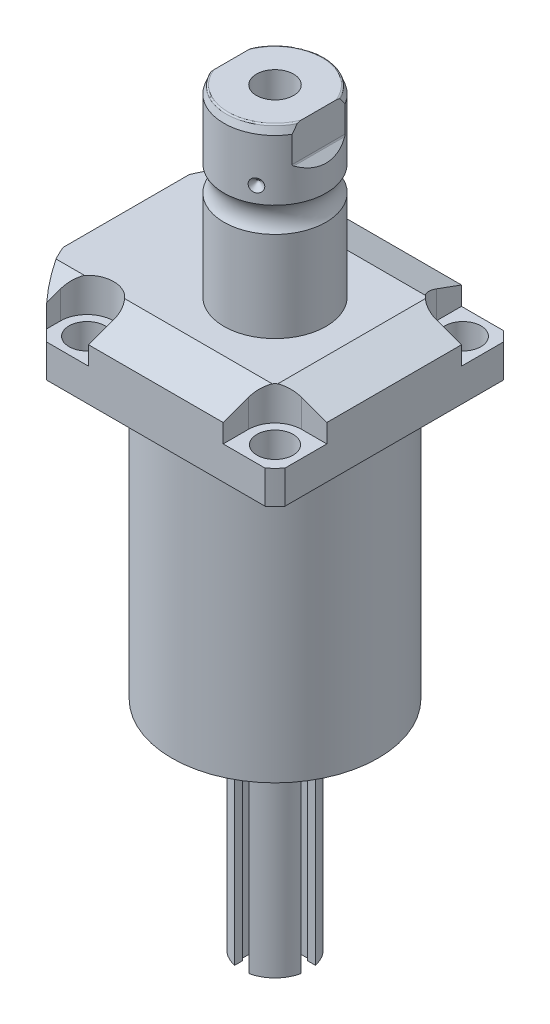
SolidWorks part; units mm, degrees
material "Alloy Steel"
ref_plane "Front Plane" through (0, 0, 0) normal (0, 0, 1) x (1, 0, 0)
ref_plane "Top Plane" through (0, 0, 0) normal (0, 1, 0) x (1, 0, 0)
ref_plane "Right Plane" through (0, 0, 0) normal (1, 0, 0) x (0, 0, -1)
ref_plane "Plane1" through (0, 0, 0) normal (0, 1, 0) x (0, 0, 1)
sketch "Sketch1" plane through (0, 0, 0) normal (0, 1, 0) x (0, 0, 1)
  line L0 (-44.45, 44.45) -> (44.45, 44.45)
  line L1 (44.45, 44.45) -> (44.45, -55.5498)
  line L2 (44.45, -55.5498) -> (-44.45, -55.5498)
  line L3 (-44.45, -55.5498) -> (-44.45, 44.45)
  line L4 (0, 0) -> (0, -60.6467) construction
  dimension "D1" = 55.5498
  dimension "D2" = 99.9998
  dimension "D3" = 88.9
extrude "Extrude1" add sketch "Sketch1" along normal blind 129.794
sketch "Sketch2" plane through (0, 0, 0) normal (0, -1, 0) x (1, 0, 0)
  circle A0 centre (0, 0) radius 60.325
  dimension "D1" = 120.65
extrude "Cut-Extrude1" cut sketch "Sketch2" against normal through all flip side to cut
ref_plane "Plane2" through (0, 0, 0) normal (1, 0, 0) x (0, 0, 1)
sketch "Sketch3" plane through (0, 0, 0) normal (1, 0, 0) x (0, 0, 1)
  line L0 (38.4937, 0) -> (38.4937, -104.775)
  line L1 (38.4937, -104.775) -> (76.5937, -104.775)
  line L2 (76.5937, -104.775) -> (76.5937, 0)
  line L3 (76.5937, 0) -> (38.4937, 0)
  line L4 (0, -93.345) -> (0, 4.445) construction
  line L5 (40.7836, 0) -> (-40.7836, 0) construction
  dimension "D1" = 76.9874
  dimension "D2" = 153.1874
  dimension "D3" = 104.775
revolve "Cut-Revolve1" cut sketch "Sketch3" angle 360 about L4
fillet "Fillet1" radius 0.381 1 edges at (0, 104.775, 38.4937)
sketch "Sketch4" plane through (0, 129.794, 0) normal (0, 1, 0) x (-1, 0, 0)
  line L0 (-44.45, 40.7836) -> (-44.45, -40.7836) construction
  line L1 (40.7836, 44.45) -> (-40.7836, 44.45) construction
  line L2 (-25.1206, -44.45) -> (-25.1206, -35.052)
  line L3 (-44.45, -44.45) -> (-25.1206, -44.45)
  line L4 (-44.45, -25.1206) -> (-44.45, -44.45)
  line L5 (-35.052, -25.1206) -> (-44.45, -25.1206)
  line L6 (44.9834, -44.45) -> (25.1206, -44.45)
  line L7 (25.1206, 44.45) -> (25.1206, 35.052)
  line L8 (44.9834, 44.45) -> (44.9834, 35.052)
  line L9 (44.9834, 44.45) -> (25.1206, 44.45)
  line L10 (-35.052, 25.1206) -> (-44.45, 25.1206)
  line L11 (-44.45, 25.1206) -> (-44.45, 44.45)
  line L12 (-44.45, 44.45) -> (-25.1206, 44.45)
  line L13 (-25.1206, 44.45) -> (-25.1206, 35.052)
  line L14 (-48.9217, 0) -> (49.4551, 0) construction
  line L15 (44.9834, -44.45) -> (44.9834, -35.052)
  line L16 (25.1206, -44.45) -> (25.1206, -35.052)
  arc A0 (25.1206, -35.052) -> (44.9834, -35.052) centre (35.052, -35.052) cw
  arc A1 (-35.052, -25.1206) -> (-25.1206, -35.052) centre (-35.052, -35.052) cw
  arc A2 (-35.052, 25.1206) -> (-25.1206, 35.052) centre (-35.052, 35.052) ccw
  arc A3 (25.1206, 35.052) -> (44.9834, 35.052) centre (35.052, 35.052) ccw
  dimension "D2" = 9.9314
  dimension "D1" = 35.052
  dimension "D3" = 35.052
  dimension "D4" = 35.052
extrude "Cut-Extrude2" cut sketch "Sketch4" against normal blind 12.7
ref_plane "Plane3" through (0, 0, 0) normal (1, 0, 0) x (0, 0, -1)
sketch "Sketch5" plane through (0, 0, 0) normal (1, 0, 0) x (0, 0, -1)
  line L0 (-28.575, 129.794) -> (-44.45, 124.016)
  line L1 (0, 0) -> (0, 154.1081) construction
  line L2 (-28.575, 129.794) -> (-44.45, 129.794)
  line L3 (-44.45, 129.794) -> (-44.45, 124.016)
  dimension "D1" = 15.875
  dimension "D2" = 20
extrude "Cut-Extrude9" cut sketch "Sketch5" against normal through all and the other way through all
mirror "Mirror1" about plane through (0, 0, 0) normal (0, 0, 1) of "Cut-Extrude9"
ref_plane "Plane7" through (0, 0, 0) normal (0, 0, 1) x (1, 0, 0)
sketch "Sketch9" plane through (0, 0, 0) normal (0, 0, 1) x (1, 0, 0)
  line L0 (28.575, 129.794) -> (44.45, 124.016)
  line L1 (44.45, 124.016) -> (44.45, 129.794)
  line L2 (44.45, 129.794) -> (28.575, 129.794)
  dimension "D1" = 15.875
  dimension "D2" = 20
extrude "Cut-Extrude7" cut sketch "Sketch9" against normal through all and the other way through all
ref_plane "Plane8" through (-41.402, 88.9, -18.1102) normal (1, 0, 0) x (0, 1, 0)
sketch "Sketch20" plane through (-41.402, 88.9, -18.1102) normal (1, 0, 0) x (0, 1, 0)
  line L0 (-88.9, 18.1102) -> (39.8401, 18.1102) construction
  line L1 (-7.2797, 36.2204) -> (36.9042, 36.2204) construction
  line L2 (15.875, 41.9227) -> (17.3228, 41.9227)
  line L3 (15.875, 58.8938) -> (15.875, -22.6734) construction
  line L4 (17.3228, 41.9227) -> (17.3228, 39.4716)
  line L5 (17.3228, 39.4716) -> (18.3388, 39.4716)
  line L6 (18.3388, 39.4716) -> (18.3388, 37.465)
  line L7 (18.3388, 37.465) -> (29.3116, 37.465)
  line L8 (29.3116, 37.465) -> (29.3116, 36.2204)
  line L9 (29.3116, 36.2204) -> (15.875, 36.2204)
  line L10 (15.875, 41.9227) -> (15.875, 36.2204)
  dimension "D1" = 18.1102
  dimension "D2" = 11.4046
  dimension "D3" = 1.4478
  dimension "D4" = 6.5024
  dimension "D5" = 1.016
  dimension "D6" = 2.4892
  dimension "D7" = 10.9728
revolve "Cut-Revolve4" cut sketch "Sketch20" angle 360 about L1
mirror "Mirror10" about plane through (0, 0, 0) normal (0, 0, 1) of "Cut-Revolve4"
sketch "Sketch10" plane through (-41.402, 88.9, -18.1102) normal (1, 0, 0) x (0, 1, 0)
  line L0 (-1.0325, 0) -> (1.5659, 0) construction
  line L1 (29.3116, 1.2446) -> (18.3388, 1.2446) construction
  line L2 (18.3388, -1.2446) -> (29.3116, -1.2446) construction
  line L3 (15.875, 58.8938) -> (15.875, -22.6734) construction
  circle A0 centre (16.1417, 4.5212) radius 1.1811
  dimension "D1" = 2.3622
  dimension "D2" = 0.2667
  dimension "D3" = 9.0424
revolve "Revolve4" add sketch "Sketch10" angle 360 about L0
ref_plane "Plane9" through (-41.402, 88.9, 18.1102) normal (1, 0, 0) x (0, 1, 0)
sketch "Sketch11" plane through (-41.402, 88.9, 18.1102) normal (1, 0, 0) x (0, 1, 0)
  line L0 (-1.0325, 0) -> (1.5659, 0) construction
  line L1 (29.3116, 1.2446) -> (18.3388, 1.2446) construction
  line L3 (15.875, 22.6734) -> (15.875, -58.8938) construction
  line L4 (18.3388, -1.2446) -> (29.3116, -1.2446) construction
  circle A0 centre (16.1417, 4.5212) radius 1.1811
  dimension "D1" = 2.3622
  dimension "D2" = 9.0424
  dimension "D3" = 0.2667
revolve "Revolve2" add sketch "Sketch11" angle 360 about L0
ref_plane "Plane10" through (-55.5498, 101.9048, 12.9794) normal (0, 0, 1) x (0, 1, 0)
sketch "S2D0007" plane through (-55.5498, 101.9048, 12.9794) normal (0, 0, 1) x (0, 1, 0)
  line L0 (15.875, 0) -> (26.3525, 0)
  line L1 (26.3525, 0) -> (26.3525, -0.254)
  line L2 (26.3525, -0.254) -> (22.0599, -0.254)
  line L3 (22.0599, -0.254) -> (21.5173, -2.8067)
  line L4 (21.5173, -2.8067) -> (20.8534, -3.4706)
  line L5 (20.8534, -3.4706) -> (20.8534, -14.224)
  line L6 (20.8534, -14.224) -> (15.875, -14.224)
  line L7 (15.875, -14.224) -> (15.875, 0)
  line L8 (15.875, -1000) -> (15.875, 49000) construction
  line L9 (2.8702, 0) -> (2.8702, -14.7662) construction
  dimension "D1" = 0.254
  dimension "D2" = 13.0048
  dimension "D3" = 9.9568
  dimension "D4" = 20.955
  dimension "D5" = 12.3698
  dimension "D6" = 12
  dimension "D7" = 45
  dimension "D8" = 13.97
  dimension "D9" = 2.5527
revolve "Cut-Revolve2" cut sketch "S2D0007" angle 360 about L8
ref_plane "Plane11" through (-55.5498, 101.9048, -12.9794) normal (0, 0, 1) x (0, 1, 0)
sketch "Sketch13" plane through (-55.5498, 101.9048, -12.9794) normal (0, 0, 1) x (0, 1, 0)
  line L0 (15.875, 0) -> (26.3525, 0)
  line L1 (26.3525, 0) -> (26.3525, -0.254)
  line L2 (26.3525, -0.254) -> (22.0599, -0.254)
  line L3 (22.0599, -0.254) -> (21.5173, -2.8067)
  line L4 (21.5173, -2.8067) -> (20.8534, -3.4706)
  line L5 (20.8534, -3.4706) -> (20.8534, -14.224)
  line L6 (20.8534, -14.224) -> (15.875, -14.224)
  line L7 (15.875, -14.224) -> (15.875, 0)
  line L8 (15.875, -1000) -> (15.875, 49000) construction
  line L9 (2.8702, 0) -> (2.8702, -14.7662) construction
  dimension "D1" = 0.254
  dimension "D2" = 13.0048
  dimension "D3" = 20.955
  dimension "D4" = 12.3698
  dimension "D5" = 12
  dimension "D6" = 45
  dimension "D7" = 2.5527
  dimension "D8" = 13.97
  dimension "D9" = 9.9568
revolve "Cut-Revolve3" cut sketch "Sketch13" angle 360 about L8
ref_plane "Plane12" through (0, 0, 0) normal (1, 0, 0) x (0, -1, 0)
sketch "Sketch15" plane through (0, 0, 0) normal (1, 0, 0) x (0, -1, 0)
  line L0 (-129.794, 0) -> (-129.794, 19.05)
  line L1 (-129.794, 19.05) -> (-163.4663, 19.05)
  line L2 (-172.8805, 19.05) -> (-195.4276, 19.05)
  line L3 (-198.3486, 17.9868) -> (-198.3486, 0)
  line L4 (-198.3486, 0) -> (-129.794, 0)
  line L5 (-197.6361, 0) -> (-64.6704, 0) construction
  line L6 (-129.794, 27.5233) -> (-129.794, -27.5233) construction
  line L7 (-104.775, 40.7836) -> (-104.775, 44.45) construction
  line L8 (-198.3486, 17.9868) -> (-195.4276, 19.05)
  arc A0 (-172.8805, 19.05) -> (-163.4663, 19.05) centre (-168.1734, 25.4254) ccw
  dimension "D2" = 20
  dimension "D4" = 7.9248
  dimension "D6" = 35.0012
  dimension "D1" = 93.5736
  dimension "D3" = 38.1
  dimension "D5" = 30.1752
  dimension "D7" = 2.921
revolve "Revolve3" add sketch "Sketch15" angle 360 about L5
ref_plane "Plane13" through (0, 0, 0) normal (0, 0, -1) x (0, -1, 0)
sketch "Sketch16" plane through (0, 0, 0) normal (0, 0, -1) x (0, -1, 0)
  line L0 (-198.3486, 19.05) -> (-182.5644, 19.05)
  line L1 (-198.3486, -19.05) -> (-198.3486, -16.2814)
  line L2 (-198.3486, 16.2814) -> (-185.6486, 16.2814)
  line L3 (-185.1098, 16.5046) -> (-182.5644, 19.05)
  line L4 (-185.1098, -16.5046) -> (-182.5644, -19.05)
  line L5 (-198.3486, -16.2814) -> (-185.6486, -16.2814)
  line L6 (-198.3486, 19.05) -> (-198.3486, 16.2814)
  line L7 (-198.3486, -19.05) -> (-182.5644, -19.05)
  line L8 (-194.0458, 0) -> (-125.0021, 0) construction
  line L11 (-198.3486, 17.9868) -> (-198.3486, -17.9868) construction
  line L12 (-172.8805, 19.05) -> (-195.4276, 19.05) construction
  arc A0 (-185.6486, 16.2814) -> (-185.1098, 16.5046) centre (-185.6486, 17.0434) ccw
  arc A1 (-185.6486, -16.2814) -> (-185.1098, -16.5046) centre (-185.6486, -17.0434) cw
  point P3 (-185.333, 16.2814)
  dimension "D4" = 0.762
  dimension "D1" = 32.5628
  dimension "D2" = 45
  dimension "D3" = 12.7
extrude "Cut-Extrude8" cut sketch "Sketch16" against normal mid plane 106.68
hole_wizard "Hole1" positions "Sketch18" profile "Sketch17" legacy end condition up to next
sketch "Sketch18" plane through (0, 117.094, 0) normal (0, 1, 0) x (-1, 0, 0)
  arc A0 (44.9834, -35.052) -> (25.1206, -35.052) centre (35.052, -35.052) ccw construction
  arc A1 (25.1206, 35.052) -> (44.9834, 35.052) centre (35.052, 35.052) ccw construction
  arc A2 (-35.052, 25.1206) -> (-25.1206, 35.052) centre (-35.052, 35.052) ccw construction
  arc A3 (-25.1206, -35.052) -> (-35.052, -25.1206) centre (-35.052, -35.052) ccw construction
  point P0 (-35.052, -35.052)
  point P1 (-35.052, 35.052)
  point P3 (35.052, 35.052)
  point P5 (35.052, -35.052)
sketch "Sketch17" plane through (35.052, 117.094, -35.052) normal (1, 0, 0) x (0, 0, 1)
  line L0 (0, 0) -> (0, 12.319)
  line L1 (0, 12.319) -> (6.7437, 12.319)
  line L2 (6.7437, 12.319) -> (6.7437, 0)
  line L3 (6.7437, 0) -> (0, 0)
  line L4 (0, 110) -> (0, -10) construction
  dimension "Diameter" = 13.4874
  dimension "Depth" = 12.319
chamfer "Chamfer1" distance 0.635 angle 45 2 edges at (-41.402, 107.2388, 16.8656) (-41.402, 107.2388, -16.8656)
sketch "Sketch21" plane through (0, 0, 0) normal (0, 0, 1) x (1, 0, 0)
  line L0 (0, 0) -> (0, 194.0957) construction
  line L1 (0, 172.9486) -> (6.9342, 177.1151)
  line L2 (6.9342, 177.1151) -> (6.9342, 198.3486)
  line L4 (6.9342, 198.3486) -> (0, 198.3486)
  line L5 (0, 198.3486) -> (0, 172.9486)
  line L6 (16.2814, 198.3486) -> (-16.2814, 198.3486) construction
  dimension "D1" = 13.8684
  dimension "D2" = 59
  dimension "D3" = 25.4
revolve "Cut-Revolve5" cut sketch "Sketch21" angle 360 about L0
fillet "Fillet2" radius 0.635 2 edges at (0, 198.3486, 17.9868) (0, 198.3486, -17.9868)
sketch "Sketch22" plane through (0, 0, 0) normal (0, 0, 1) x (1, 0, 0)
  line L0 (-37.9974, 178.8414) -> (37.12, 178.8414) construction
  line L1 (-19.05, 181.2544) -> (-16.637, 178.8414)
  line L2 (-16.637, 178.8414) -> (-19.05, 178.8414)
  line L3 (-19.05, 178.8414) -> (-19.05, 181.2544)
  line L4 (-19.05, 182.5644) -> (-19.05, 172.8805) construction
  arc A0 (-19.05, 163.4663) -> (-19.05, 172.8805) centre (-25.4254, 168.1734) ccw construction
  dimension "D2" = 10.668
  dimension "D1" = 4.826
  dimension "D3" = 45
revolve "Cut-Revolve6" cut sketch "Sketch22" angle 360 about L0
pattern_circular "CirPattern1" count 3 over 360 about axis through (0, 197.6361, 0) along (0, 1, 0) of "Cut-Revolve6"
sketch "Sketch23" plane through (0, 0, 0) normal (0, 0, 1) x (1, 0, 0)
  line L0 (0, -1000) -> (0, 49000) construction
  line L1 (0, 0) -> (22.225, 0)
  line L2 (-38.4937, 0) -> (38.4937, 0) construction
  line L3 (22.225, 0) -> (22.225, -2.54)
  line L4 (22.225, -2.54) -> (12.7, -2.54)
  line L5 (12.7, -2.54) -> (12.7, -81.28)
  line L6 (12.7, -81.28) -> (0, -81.28)
  line L7 (0, -81.28) -> (0, 0)
  dimension "D1" = 44.45
  dimension "D2" = 25.4
  dimension "D3" = 2.54
  dimension "D4" = 81.28
revolve "Revolve5" add sketch "Sketch23" angle 360 about L0
sketch "Sketch24" plane through (0, -2.54, 0) normal (0, -1, 0) x (1, 0, 0)
  line L0 (-1000, 0) -> (49000, 0) construction
  line L1 (0, -1000) -> (0, 49000) construction
  line L2 (0, 0) -> (43301.2702, 25000) construction
  line L3 (0, 0) -> (25000, 43301.2702) construction
  circle A0 centre (0, 0) radius 19.431 construction
  circle A1 centre (19.431, 0) radius 1.7272
  circle A2 centre (16.8277, 9.7155) radius 1.7272
  circle A3 centre (9.7155, 16.8277) radius 1.7272
  circle A4 centre (0, 19.431) radius 1.7272
  circle A5 centre (-9.7155, 16.8277) radius 1.7272
  circle A6 centre (-16.8277, 9.7155) radius 1.7272
  circle A7 centre (-19.431, 0) radius 1.7272
  circle A8 centre (-16.8277, -9.7155) radius 1.7272
  circle A9 centre (-9.7155, -16.8277) radius 1.7272
  circle A10 centre (0, -19.431) radius 1.7272
  circle A11 centre (9.7155, -16.8277) radius 1.7272
  circle A12 centre (16.8277, -9.7155) radius 1.7272
  dimension "D3" = 38.862
  dimension "D4" = 3.4544
  dimension "D5" = 3.4544
  dimension "D6" = 3.4544
  dimension "D7" = 3.4544
  dimension "D1" = 30
  dimension "D2" = 30
extrude "Cut-Extrude10" cut sketch "Sketch24" against normal up to surface (2.54 mm away) up to face at (0, 0, -22.225)
sketch "Sketch25" plane through (0, -2.54, 0) normal (0, -1, 0) x (1, 0, 0)
  circle A0 centre (19.431, 0) radius 2.7051
  circle A1 centre (-9.7155, 16.8277) radius 2.7051
  circle A2 centre (-9.7155, -16.8277) radius 2.7051
  dimension "D1" = 5.4102
  dimension "D2" = 5.4102
  dimension "D3" = 5.4102
extrude "Extrude2" add sketch "Sketch25" along normal blind 2.9464
ref_plane "Plane15-slot-angle" through (0, 0, 0) normal (1, 0, 0) x (0, 0, -1)
ref_plane "Plane16" through (0, -41.91, 12.7) normal (0, 0, 1) x (-1, 0, 0)
sketch "Sketch31" plane through (0, -41.91, 12.7) normal (0, 0, 1) x (-1, 0, 0)
  line L0 (0, -1034.036) -> (0, 48965.964) construction
  line L1 (0, -1034.036) -> (0, 48965.964) construction
  line L2 (-2.6416, -28.9574) -> (-2.6416, 39.37)
  line L3 (12.7, 39.37) -> (-12.7, 39.37) construction
  line L4 (-2.6416, 39.37) -> (2.6416, 39.37)
  line L5 (2.6416, -28.9574) -> (2.6416, 39.37)
  arc A0 (-2.6416, -28.9574) -> (2.6416, -28.9574) centre (0, -31.242) ccw
  point P14 (0, 39.37)
  dimension "D1" = 6.985
  dimension "D2" = 5.2832
  dimension "D3" = 70.612
extrude "Cut-Extrude11" cut sketch "Sketch31" against normal blind 6.477
sketch "Sketch32" plane through (0, 0, 6.223) normal (0, 0, 1) x (1, 0, 0)
  line L0 (0, -1000) -> (0, 49000) construction
  line L1 (3.4925, -10.668) -> (3.4925, -81.28)
  line L2 (-12.7, -81.28) -> (12.7, -81.28) construction
  line L3 (3.4925, -81.28) -> (-3.4925, -81.28)
  line L4 (-2.6416, -81.28) -> (2.6416, -81.28) construction
  line L5 (3.4925, -10.668) -> (-3.4925, -10.668)
  line L6 (-3.4925, -10.668) -> (-3.4925, -81.28)
  point P13 (0, -81.28)
  point P14 (0, -10.668)
  dimension "D1" = 6.985
extrude "Cut-Extrude12" cut sketch "Sketch32" along normal blind 3.302
ref_plane "Plane17" through (0, 0, 0) normal (0, 0, 1) x (1, 0, 0)
mirror "Mirror11" about plane through (0, 0, 0) normal (0, 0, 1) of "Cut-Extrude12", "Cut-Extrude11"
sketch "Sketch35" plane through (0, -5.4864, 0) normal (0, -1, 0) x (1, 0, 0)
  line L1 (19.431, -1.4371) -> (20.6756, -0.7186)
  line L2 (20.6756, -0.7186) -> (20.6756, 0.7186)
  line L3 (20.6756, 0.7186) -> (19.431, 1.4371)
  line L4 (19.431, 1.4371) -> (18.1864, 0.7186)
  line L5 (18.1864, 0.7186) -> (18.1864, -0.7186)
  line L6 (18.1864, -0.7186) -> (19.431, -1.4371)
  line L7 (-9.2553, 15.4663) -> (-8.3063, 16.5455)
  line L8 (-8.3063, 16.5455) -> (-8.7665, 17.907)
  line L9 (-8.7665, 17.907) -> (-10.1757, 18.1892)
  line L10 (-10.1757, 18.1892) -> (-11.1247, 17.1099)
  line L11 (-11.1247, 17.1099) -> (-10.6645, 15.7485)
  line L12 (-10.6645, 15.7485) -> (-9.2553, 15.4663)
  line L13 (-9.7155, -18.2649) -> (-8.4709, -17.5463)
  line L14 (-8.4709, -17.5463) -> (-8.4709, -16.1092)
  line L15 (-8.4709, -16.1092) -> (-9.7155, -15.3906)
  line L16 (-9.7155, -15.3906) -> (-10.9601, -16.1092)
  line L17 (-10.9601, -16.1092) -> (-10.9601, -17.5463)
  line L18 (-10.9601, -17.5463) -> (-9.7155, -18.2649)
  circle A0 centre (19.431, 0) radius 1.2446 construction
  circle A1 centre (-9.7155, 16.8277) radius 1.2446 construction
  circle A2 centre (-9.7155, -16.8277) radius 1.2446 construction
  dimension "D1" = 2.4892
  dimension "D2" = 2.4892
  dimension "D3" = 2.4892
extrude "Cut-Extrude13" cut sketch "Sketch35" against normal blind 2.032
pattern_circular "CirPattern2" count 2 every 90 about axis through (0, 0, 0) along (0, 1, 0) of "Mirror11", "Cut-Extrude11", "Cut-Extrude12"
